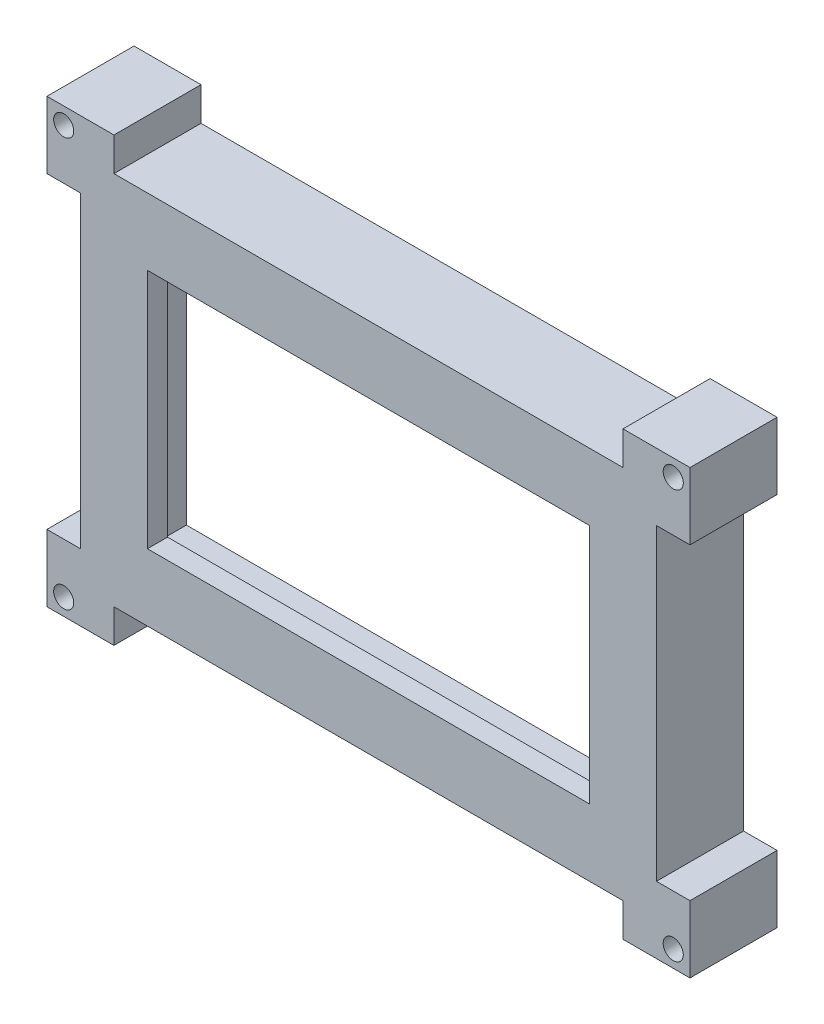
SolidWorks part; units mm, degrees
ref_plane "Front Plane" through (0, 0, 0) normal (0, 0, 1) x (1, 0, 0)
ref_plane "Top Plane" through (0, 0, 0) normal (0, 1, 0) x (1, 0, 0)
ref_plane "Right Plane" through (0, 0, 0) normal (1, 0, 0) x (0, 0, -1)
sketch "Sketch1" plane through (0, 0, 0) normal (0, 0, 1) x (1, 0, 0)
  line L0 (-40.8166, 20.9928) -> (-40.8166, -35.0072)
  line L1 (-37.8166, 17.9928) -> (42.1834, 17.9928)
  line L2 (-37.8166, 17.9928) -> (-37.8166, -32.0072)
  line L3 (-37.8166, -32.0072) -> (42.1834, -32.0072)
  line L4 (42.1834, 17.9928) -> (42.1834, -32.0072)
  line L5 (-40.8166, -35.0072) -> (45.1834, -35.0072)
  line L6 (45.1834, 20.9928) -> (45.1834, -35.0072)
  line L7 (-40.8166, 20.9928) -> (45.1834, 20.9928)
  dimension "D1" = 80
  dimension "D2" = 50
  dimension "D3" = 3
extrude "Boss-Extrude1" add sketch "Sketch1" along normal blind 10
sketch "Sketch2" plane through (0, 0, 10) normal (0, 0, 1) x (1, 0, 0)
  line L0 (45.1834, -35.0072) -> (45.1834, 20.9928) construction
  line L1 (-40.8166, -35.0072) -> (45.1834, -35.0072) construction
  line L2 (-40.8166, 20.9928) -> (-40.8166, -35.0072) construction
  line L3 (45.1834, 20.9928) -> (-40.8166, 20.9928) construction
  line L4 (45.1834, -35.0072) -> (45.1834, 20.9928)
  line L5 (-40.8166, -35.0072) -> (45.1834, -35.0072)
  line L6 (-40.8166, 20.9928) -> (-40.8166, -35.0072)
  line L7 (45.1834, 20.9928) -> (-40.8166, 20.9928)
extrude "Boss-Extrude2" add sketch "Sketch2" along normal blind 3
sketch "Sketch3" plane through (0, 0, 13) normal (0, 0, 1) x (1, 0, 0)
  line L0 (-40.8166, -35.0072) -> (45.1834, -35.0072) construction
  line L1 (-30.8166, 10.9928) -> (35.1834, 10.9928)
  line L2 (-30.8166, 10.9928) -> (-30.8166, -25.0072)
  line L3 (-30.8166, -25.0072) -> (35.1834, -25.0072)
  line L4 (35.1834, 10.9928) -> (35.1834, -25.0072)
  line L5 (45.1834, -35.0072) -> (45.1834, 20.9928) construction
  line L6 (45.1834, 20.9928) -> (-40.8166, 20.9928) construction
  line L7 (-40.8166, 20.9928) -> (-40.8166, -35.0072) construction
  dimension "D1" = 10
  dimension "D2" = 10
  dimension "D3" = 10
  dimension "D4" = 10
extrude "Cut-Extrude1" cut sketch "Sketch3" against normal through all both and the other way through all
sketch "Sketch4" plane through (0, 0, 13) normal (0, 0, 1) x (1, 0, 0)
  line L1 (-45.8166, -40.0072) -> (-35.8166, -40.0072)
  line L2 (-45.8166, -40.0072) -> (-45.8166, -30.0072)
  line L3 (-45.8166, -30.0072) -> (-35.8166, -30.0072)
  line L4 (-35.8166, -40.0072) -> (-35.8166, -30.0072)
  line L5 (-45.8166, -40.0072) -> (-35.8166, -30.0072) construction
  line L6 (-45.8166, -30.0072) -> (-35.8166, -40.0072) construction
  line L7 (-40.8166, 20.9928) -> (-40.8166, -35.0072) construction
  line L8 (-40.8166, -35.0072) -> (45.1834, -35.0072) construction
  circle A0 centre (-43.3166, -37.5072) radius 1.5
  point P0 (-40.8166, 20.9928)
  point P1 (-40.8166, -35.0072)
  point P10 (-35.8166, -35.0072)
  dimension "D3" = 3
  dimension "D1" = 5
  dimension "D2" = 5
  dimension "D4" = 2.5
extrude "Boss-Extrude4" add sketch "Sketch4" against normal up to surface (13 mm away) up to face at (2.1834, -7.0072, 0)
ref_plane "Plane3" through (2.1834, 0, 0) normal (-1, 0, 0) x (0, 0, 1)
ref_plane "Plane4" through (0, -7.0072, 0) normal (0, -1, 0) x (-1, 0, 0)
mirror "Mirror5" about plane through (2.1834, 0, 0) normal (-1, 0, 0) of "Boss-Extrude4"
mirror "Mirror6" about plane through (0, -7.0072, 0) normal (0, -1, 0) of "Mirror5", "Boss-Extrude4"
sketch "Sketch7" plane through (0, 0, 0) normal (0, 0, -1) x (-1, 0, 0)
  line L1 (-42.1834, 17.9928) -> (37.9993, 17.9928)
  line L2 (-42.1834, 17.9928) -> (-42.1834, -32.041)
  line L3 (-42.1834, -32.041) -> (37.9993, -32.041)
  line L4 (37.9993, 17.9928) -> (37.9993, -32.041)
extrude "Cut-Extrude3" cut sketch "Sketch7" against normal up to surface (10 mm away) up to face at (2.1834, -7.0072, 10)
